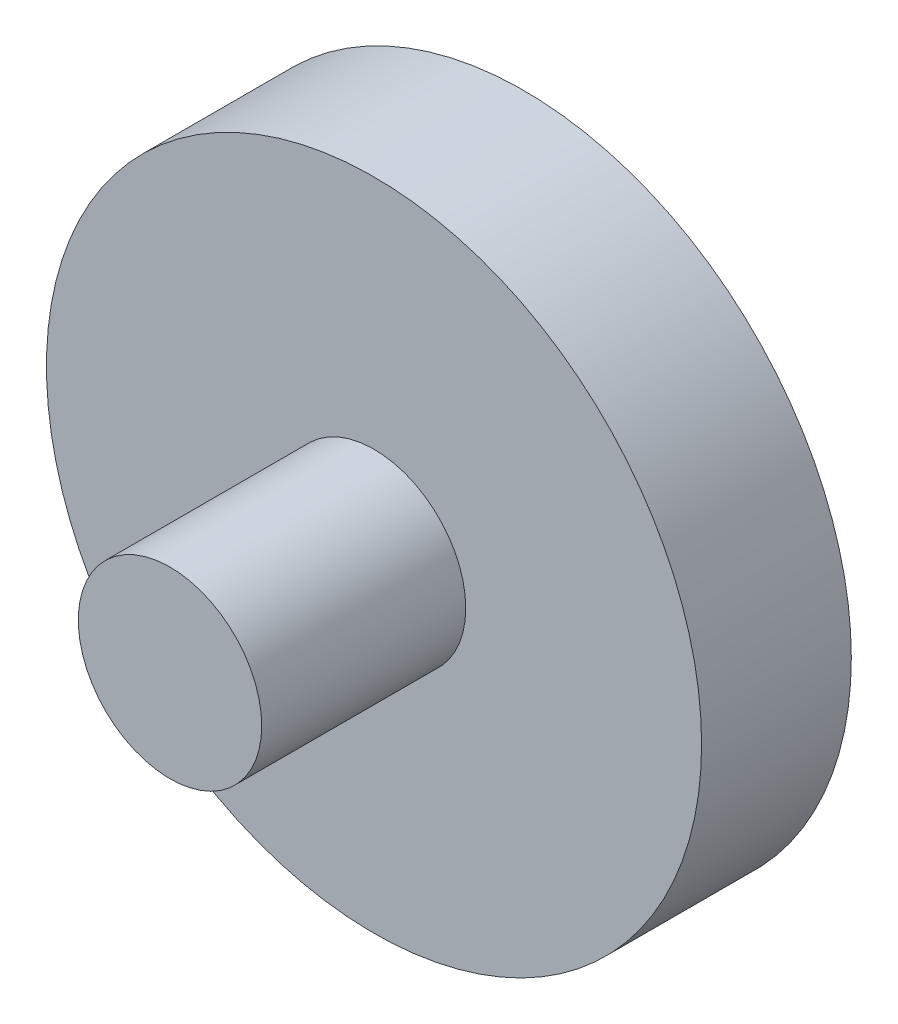
SolidWorks part; units mm, degrees
ref_plane "Front Plane" through (0, 0, 0) normal (0, 0, 1) x (1, 0, 0)
ref_plane "Top Plane" through (0, 0, 0) normal (0, 1, 0) x (1, 0, 0)
ref_plane "Right Plane" through (0, 0, 0) normal (1, 0, 0) x (0, 0, -1)
sketch "Sketch1" plane through (0, 0, 0) normal (0, 0, 1) x (1, 0, 0)
  circle A0 centre (0, 0) radius 17.5
  dimension "D1" = 35
extrude "Boss-Extrude1" add sketch "Sketch1" along normal blind 8
sketch "Sketch2" plane through (0, 0, 8) normal (0, 0, 1) x (1, 0, 0)
  circle A0 centre (0, 0) radius 4.9
  dimension "D1" = 9.8
extrude "Boss-Extrude2" add sketch "Sketch2" along normal blind 10.9
